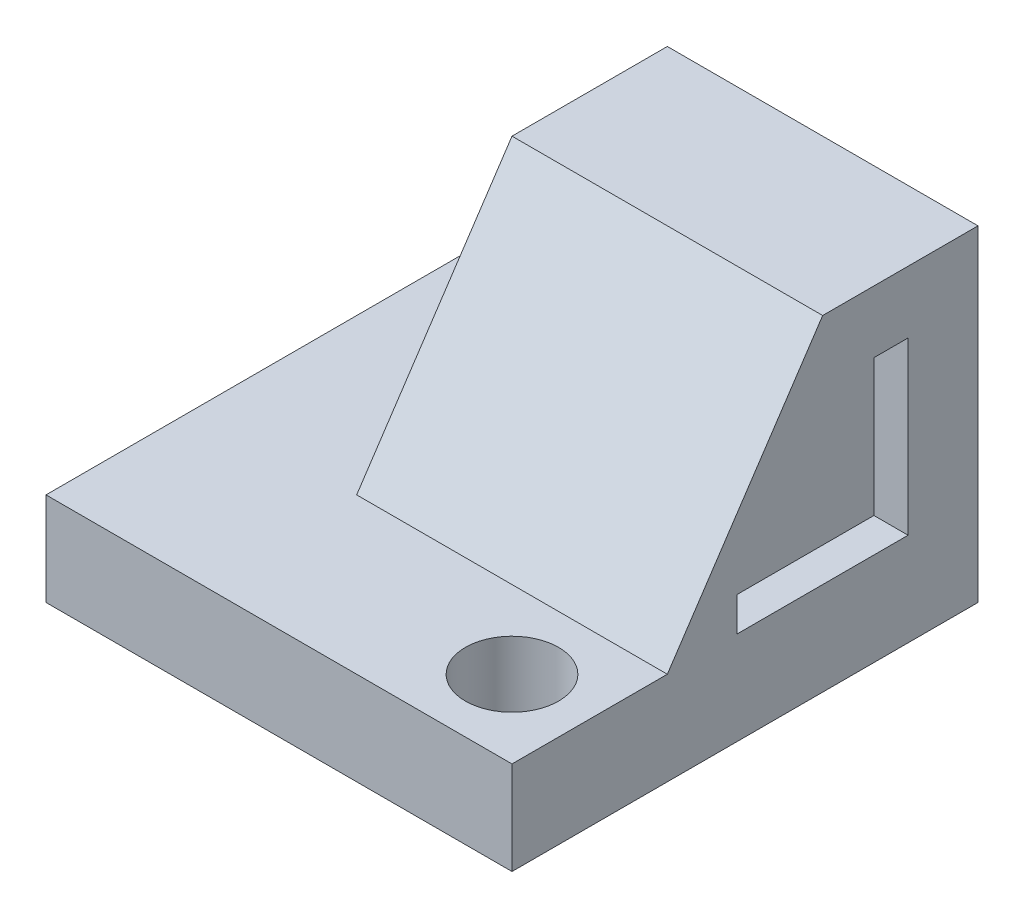
SolidWorks part; units mm, degrees
ref_plane "Front Plane" through (0, 0, 0) normal (0, 0, 1) x (1, 0, 0)
ref_plane "Top Plane" through (0, 0, 0) normal (0, 1, 0) x (1, 0, 0)
ref_plane "Right Plane" through (0, 0, 0) normal (1, 0, 0) x (0, 0, -1)
sketch "Sketch1" plane through (0, 0, 0) normal (0, 1, 0) x (1, 0, 0)
  line L1 (19.05, -19.05) -> (-19.05, -19.05)
  line L2 (19.05, -19.05) -> (19.05, 19.05)
  line L3 (19.05, 19.05) -> (-19.05, 19.05)
  line L4 (-19.05, -19.05) -> (-19.05, 19.05)
  line L5 (19.05, -19.05) -> (-19.05, 19.05) construction
  line L6 (19.05, 19.05) -> (-19.05, -19.05) construction
  point P0 (0, 0)
  dimension "D1" = 38.1
  dimension "D2" = 38.1
extrude "Boss-Extrude1" add sketch "Sketch1" along normal blind 7.62
sketch "Sketch2" plane through (0, 7.62, 0) normal (0, 1, 0) x (1, 0, 0)
  line L0 (19.05, 19.05) -> (-19.05, 19.05) construction
  line L1 (19.05, -6.35) -> (-6.35, -6.35)
  line L2 (19.05, -6.35) -> (19.05, 19.05)
  line L3 (19.05, 19.05) -> (-6.35, 19.05)
  line L4 (-6.35, -6.35) -> (-6.35, 19.05)
  line L5 (19.05, -6.35) -> (-6.35, 19.05) construction
  line L6 (19.05, 19.05) -> (-6.35, -6.35) construction
  line L7 (19.05, -19.05) -> (19.05, 19.05) construction
  point P0 (6.35, 6.35)
  dimension "D1" = 25.4
  dimension "D2" = 25.4
extrude "Boss-Extrude2" add sketch "Sketch2" along normal blind 19.05
sketch "Sketch3" plane through (0, 7.62, 0) normal (0, 1, 0) x (1, 0, 0)
  line L0 (-12.7, 12.7) -> (12.7, 12.7) construction
  line L1 (12.7, 12.7) -> (12.7, -12.7) construction
  line L2 (-12.7, 12.7) -> (-19.05, 12.7) construction
  line L3 (-19.05, 19.05) -> (-19.05, -19.05) construction
  line L4 (12.7, -12.7) -> (19.05, -12.7) construction
  line L5 (19.05, -19.05) -> (19.05, -6.35) construction
  line L6 (-12.7, 12.7) -> (-12.7, 19.05) construction
  line L9 (12.7, -12.7) -> (12.7, -19.05) construction
  line L10 (-19.05, -19.05) -> (19.05, -19.05) construction
  line L11 (-6.35, 19.05) -> (-19.05, 19.05) construction
  circle A0 centre (-12.7, 12.7) radius 3.81
  circle A1 centre (12.7, -12.7) radius 3.81
  dimension "D3" = 7.62
  dimension "D1" = 25.4
  dimension "D2" = 25.4
extrude "Cut-Extrude1" cut sketch "Sketch3" against normal up to next
sketch "Sketch4" plane through (19.05, 0, 0) normal (1, 0, 0) x (0, 0, -1)
  line L0 (10.541, 21.59) -> (13.335, 21.59)
  line L1 (13.335, 21.59) -> (13.335, 7.62)
  line L2 (13.335, 7.62) -> (-0.635, 7.62)
  line L3 (-0.635, 7.62) -> (-0.635, 10.414)
  line L4 (-0.635, 10.414) -> (10.541, 10.414)
  line L5 (10.541, 10.414) -> (10.541, 21.59)
  line L6 (-6.35, 7.62) -> (19.05, 7.62) construction
  point P7 (6.35, 7.62)
  point P11 (6.35, 7.62)
  dimension "D1" = 2.794
  dimension "D2" = 13.97
extrude "Cut-Extrude2" cut sketch "Sketch4" against normal blind 6.35
sketch "Sketch5" plane through (19.05, 0, 0) normal (1, 0, 0) x (0, 0, -1)
  line L0 (6.35, 26.67) -> (-6.35, 7.62)
  line L1 (-6.35, 26.67) -> (19.05, 26.67) construction
  line L2 (-6.35, 7.62) -> (-6.35, 26.67)
  line L3 (-6.35, 26.67) -> (6.35, 26.67)
extrude "Cut-Extrude3" cut sketch "Sketch5" against normal up to next
